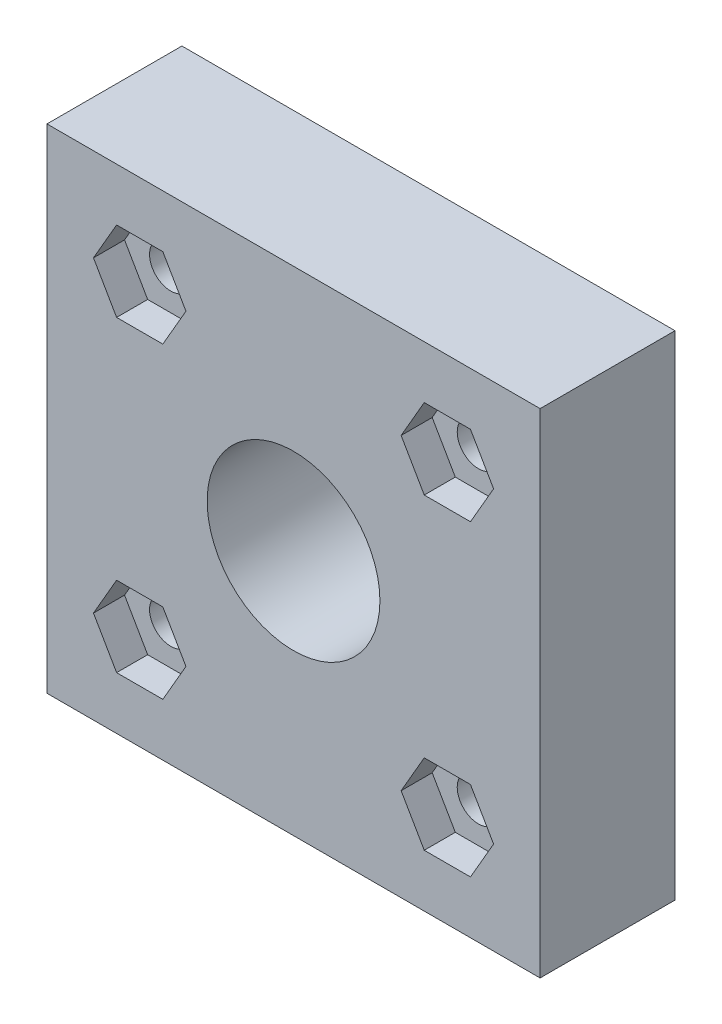
SolidWorks part; units mm, degrees
ref_plane "Front Plane" through (0, 0, 0) normal (0, 0, 1) x (1, 0, 0)
ref_plane "Top Plane" through (0, 0, 0) normal (0, 1, 0) x (1, 0, 0)
ref_plane "Right Plane" through (0, 0, 0) normal (1, 0, 0) x (0, 0, -1)
sketch "Sketch1" plane through (0, 0, 0) normal (0, 0, 1) x (1, 0, 0)
  line L1 (-12.7, 12.7) -> (12.7, 12.7)
  line L2 (-12.7, 12.7) -> (-12.7, -12.7)
  line L3 (-12.7, -12.7) -> (12.7, -12.7)
  line L4 (12.7, 12.7) -> (12.7, -12.7)
  line L5 (-12.7, 12.7) -> (12.7, -12.7) construction
  line L6 (-12.7, -12.7) -> (12.7, 12.7) construction
  point P0 (0, 0)
  dimension "D1" = 25.4
extrude "Boss-Extrude1" add sketch "Sketch1" along normal blind 1.6
sketch "Sketch2" plane through (0, 0, 1.6) normal (0, 0, 1) x (1, 0, 0)
  circle A0 centre (0, 0) radius 4.45
  dimension "D1" = 8.9
extrude "Cut-Extrude1" cut sketch "Sketch2" against normal through all
sketch "Sketch3" plane through (0, 0, 1.6) normal (0, 0, 1) x (1, 0, 0)
  line L0 (-12.7, 12.7) -> (-7.9233, 7.9233) construction
  line L1 (-7.9233, 7.9233) -> (-3.1466, 3.1466) construction
  line L2 (-3.1466, 3.1466) -> (0, 0) construction
  line L3 (0, 0) -> (0, 12.7) construction
  line L4 (12.7, 12.7) -> (-12.7, 12.7) construction
  line L5 (0, 0) -> (12.7, 0) construction
  line L6 (12.7, -12.7) -> (12.7, 12.7) construction
  line L7 (9.1139, 5.8611) -> (6.7327, 5.8611)
  line L8 (-6.7327, 5.8611) -> (-5.5421, 7.9233)
  line L9 (-5.5421, 7.9233) -> (-6.7327, 9.9855)
  line L10 (-6.7327, 9.9855) -> (-9.1139, 9.9855)
  line L11 (-9.1139, 9.9855) -> (-10.3046, 7.9233)
  line L12 (-10.3046, 7.9233) -> (-9.1139, 5.8611)
  line L13 (-9.1139, 5.8611) -> (-6.7327, 5.8611)
  line L14 (10.3046, 7.9233) -> (9.1139, 5.8611)
  line L15 (9.1139, 9.9855) -> (10.3046, 7.9233)
  line L16 (6.7327, 9.9855) -> (9.1139, 9.9855)
  line L17 (5.5421, 7.9233) -> (6.7327, 9.9855)
  line L18 (6.7327, 5.8611) -> (5.5421, 7.9233)
  line L19 (6.7327, -5.8611) -> (5.5421, -7.9233)
  line L20 (5.5421, -7.9233) -> (6.7327, -9.9855)
  line L21 (6.7327, -9.9855) -> (9.1139, -9.9855)
  line L22 (9.1139, -9.9855) -> (10.3046, -7.9233)
  line L23 (10.3046, -7.9233) -> (9.1139, -5.8611)
  line L24 (-9.1139, -5.8611) -> (-6.7327, -5.8611)
  line L25 (-10.3046, -7.9233) -> (-9.1139, -5.8611)
  line L26 (-9.1139, -9.9855) -> (-10.3046, -7.9233)
  line L27 (-6.7327, -9.9855) -> (-9.1139, -9.9855)
  line L28 (-5.5421, -7.9233) -> (-6.7327, -9.9855)
  line L29 (-6.7327, -5.8611) -> (-5.5421, -7.9233)
  line L30 (9.1139, -5.8611) -> (6.7327, -5.8611)
  circle A0 centre (-7.9233, 7.9233) radius 1.0922 construction
  circle A1 centre (0, 0) radius 4.45 construction
  circle A2 centre (7.9233, 7.9233) radius 1.0922 construction
  circle A3 centre (7.9233, -7.9233) radius 1.0922 construction
  circle A4 centre (-7.9233, -7.9233) radius 1.0922 construction
  circle A5 centre (-7.9233, 7.9233) radius 2.0622 construction
  circle A6 centre (7.9233, 7.9233) radius 2.0622 construction
  circle A7 centre (7.9233, 7.9233) radius 1.0922 construction
  circle A8 centre (7.9233, -7.9233) radius 1.0922 construction
  circle A9 centre (7.9233, -7.9233) radius 2.0622 construction
  circle A10 centre (-7.9233, -7.9233) radius 2.0622 construction
  circle A11 centre (-7.9233, -7.9233) radius 1.0922 construction
  circle A12 centre (7.9233, -7.9233) radius 1.0922 construction
  dimension "D1" = 2.1844
  dimension "D2" = 4.7625
extrude "Cut-Extrude2" cut sketch "Sketch3" against normal through all
sketch "Sketch4" plane through (0, 0, 0) normal (0, 0, -1) x (-1, 0, 0)
  line L1 (-12.7, 12.7) -> (12.7, 12.7)
  line L2 (-12.7, 12.7) -> (-12.7, -12.7)
  line L3 (-12.7, -12.7) -> (12.7, -12.7)
  line L4 (12.7, 12.7) -> (12.7, -12.7)
  circle A0 centre (7.9233, -7.9233) radius 1.0922 construction
  circle A1 centre (-7.9233, -7.9233) radius 1.0922 construction
  circle A2 centre (7.9233, 7.9233) radius 1.0922 construction
  circle A3 centre (-7.9233, 7.9233) radius 1.0922 construction
  circle A4 centre (7.9233, -7.9233) radius 1.0922
  circle A5 centre (-7.9233, -7.9233) radius 1.0922
  circle A6 centre (7.9233, 7.9233) radius 1.0922
  circle A7 centre (-7.9233, 7.9233) radius 1.0922
  circle A8 centre (0, 0) radius 4.45 construction
  circle A9 centre (0, 0) radius 4.45
extrude "Boss-Extrude2" add sketch "Sketch4" along normal blind 5.35
